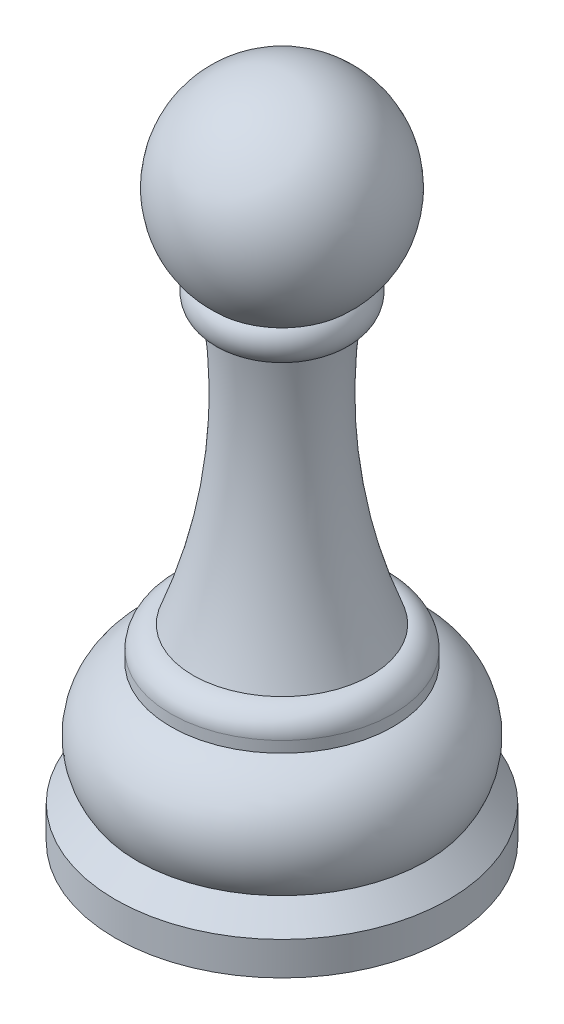
SolidWorks part; units mm, degrees
ref_plane "Front Plane" through (0, 0, 0) normal (0, 0, 1) x (1, 0, 0)
ref_plane "Top Plane" through (0, 0, 0) normal (0, 1, 0) x (1, 0, 0)
ref_plane "Right Plane" through (0, 0, 0) normal (1, 0, 0) x (0, 0, -1)
sketch "Sketch1" plane through (0, 0, 0) normal (0, 0, 1) x (1, 0, 0)
  line L0 (0, 69.1181) -> (0, -23.262) construction
  line L1 (0, 0) -> (-15, 0)
  line L2 (-15, 0) -> (-15, 3)
  line L3 (0, 5) -> (-13, 5)
  line L4 (-15, 3) -> (-13, 5)
  line L5 (0, 13.97) -> (-10, 13.97)
  line L6 (0, 14.97) -> (-10, 14.97)
  line L7 (-10, 13.97) -> (-10, 14.97)
  line L8 (0, 16.97) -> (-8, 16.97)
  line L9 (0, 41.03) -> (-5, 41.03)
  line L10 (0, 44.29) -> (-6, 44.29)
  arc A0 (-13, 5) -> (-10, 13.97) centre (-7.9981, 8.3138) cw
  arc A1 (-10, 14.97) -> (-8, 16.97) centre (-8, 14.97) cw
  arc A2 (-8, 16.97) -> (-5, 41.03) centre (-54.6353, 35.0019) ccw
  arc A3 (-5, 41.03) -> (-6, 44.29) centre (-4.5005, 42.9666) cw
  arc A4 (-6, 44.29) -> (0, 60) centre (-0.002, 51) cw
  dimension "D7" = 6
  dimension "D12" = 2
  dimension "D15" = 50
  dimension "D18" = 2
  dimension "D19" = 9
  dimension "D1" = 15
  dimension "D2" = 3
  dimension "D3" = 13
  dimension "D4" = 5
  dimension "D5" = 10
  dimension "D6" = 8.97
  dimension "D8" = 10
  dimension "D9" = 1
  dimension "D10" = 8
  dimension "D11" = 2
  dimension "D13" = 5
  dimension "D14" = 24.06
  dimension "D16" = 6
  dimension "D17" = 3.26
  dimension "D20" = 15.71
revolve "Revolve1" add sketch "Sketch1" angle 360 about L0
